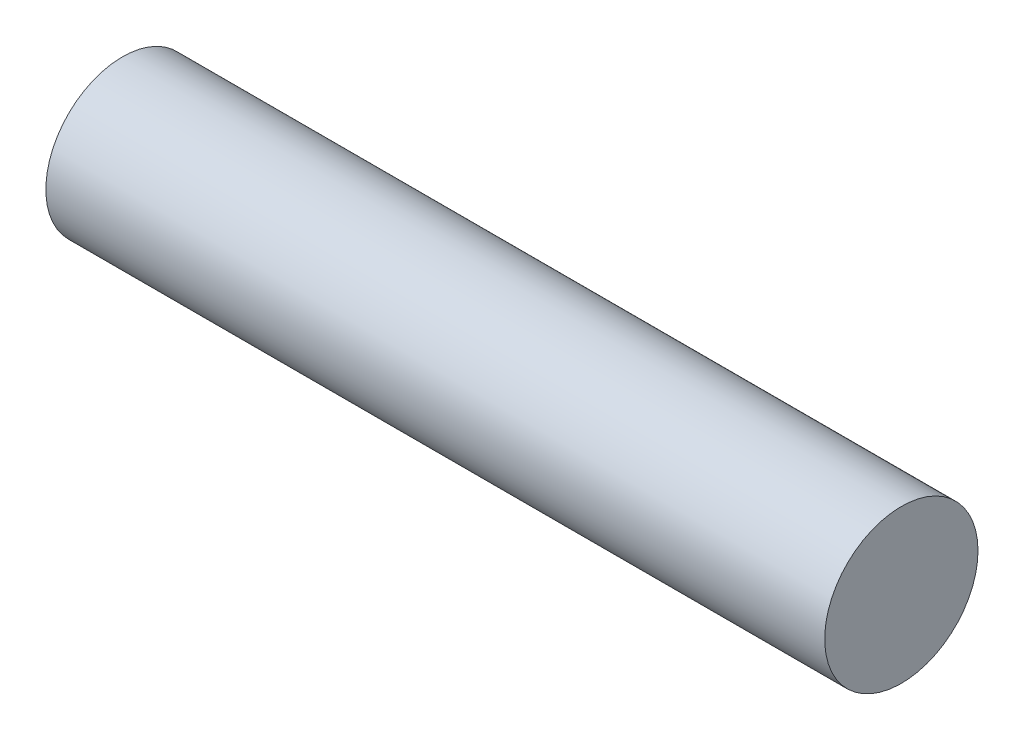
SolidWorks part; units mm, degrees
ref_plane "Front Plane" through (0, 0, 0) normal (0, 0, 1) x (1, 0, 0)
ref_plane "Top Plane" through (0, 0, 0) normal (0, 1, 0) x (1, 0, 0)
ref_plane "Right Plane" through (0, 0, 0) normal (1, 0, 0) x (0, 0, -1)
sketch "Sketch1" plane through (0, 0, 0) normal (1, 0, 0) x (0, 0, -1)
  circle A0 centre (0, 0) radius 5
  dimension "D1" = 10
extrude "Boss-Extrude1" add sketch "Sketch1" along normal mid plane 50.8
